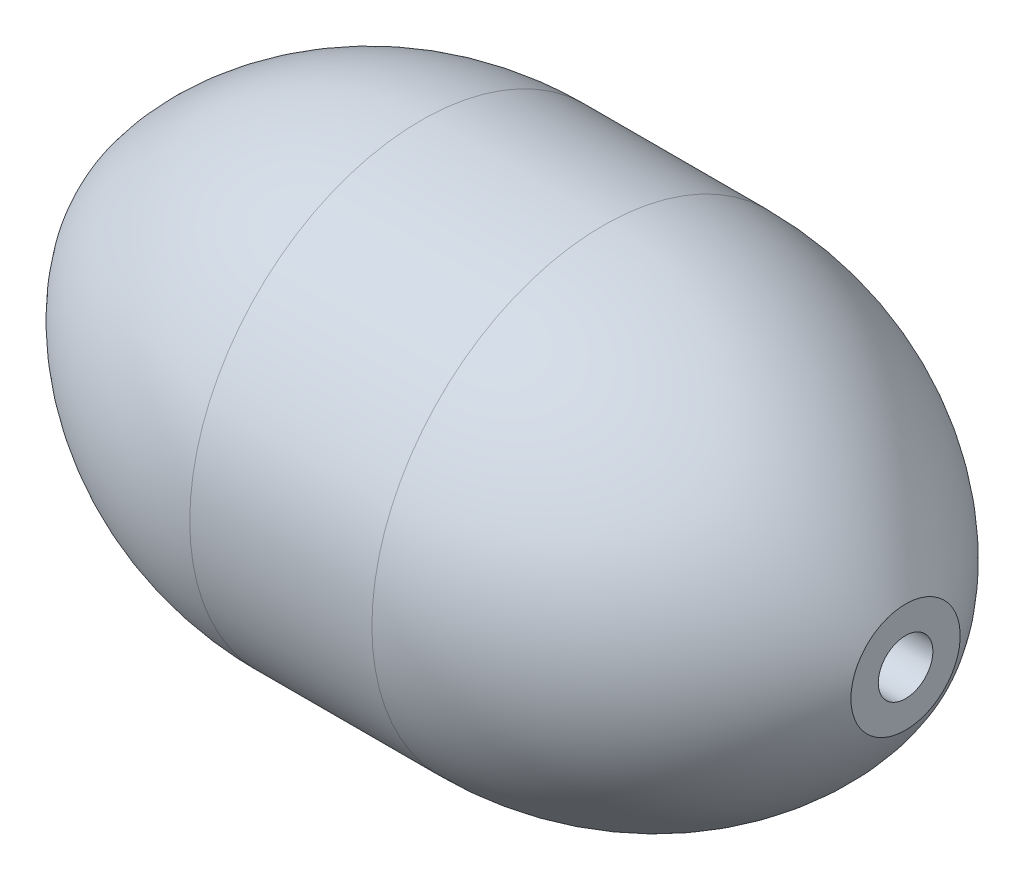
SolidWorks part; units mm, degrees
material "G-10 Glass Laminate"
ref_plane "Front Plane" through (0, 0, 0) normal (0, 0, 1) x (1, 0, 0)
ref_plane "Top Plane" through (0, 0, 0) normal (0, 1, 0) x (1, 0, 0)
ref_plane "Right Plane" through (0, 0, 0) normal (1, 0, 0) x (0, 0, -1)
sketch "Sketch1" plane through (0, 0, 0) normal (0, 0, 1) x (1, 0, 0)
  line L0 (-2.16, 0) -> (2.16, 0) construction
  line L1 (-0.5, 1.27) -> (0.5, 1.27)
  line L2 (-2.16, 0.15) -> (-2.16, 0.3)
  line L3 (2.16, 0.3) -> (2.16, 0.15)
  line L4 (-2.16, 0.15) -> (2.16, 0.15)
  line L5 (0, 0) -> (0, 1.27) construction
  arc A0 (-2.16, 0.3) -> (-0.5, 1.27) centre (-0.5, -0.6354) cw
  arc A1 (0.5, 1.27) -> (2.16, 0.3) centre (0.5, -0.6354) cw
  dimension "D4" = 1
  dimension "D1" = 4.32
  dimension "D2" = 1.27
  dimension "D3" = 0.15
  dimension "D6" = 0.15
revolve "Revolve1" add sketch "Sketch1" angle 360 about L0
